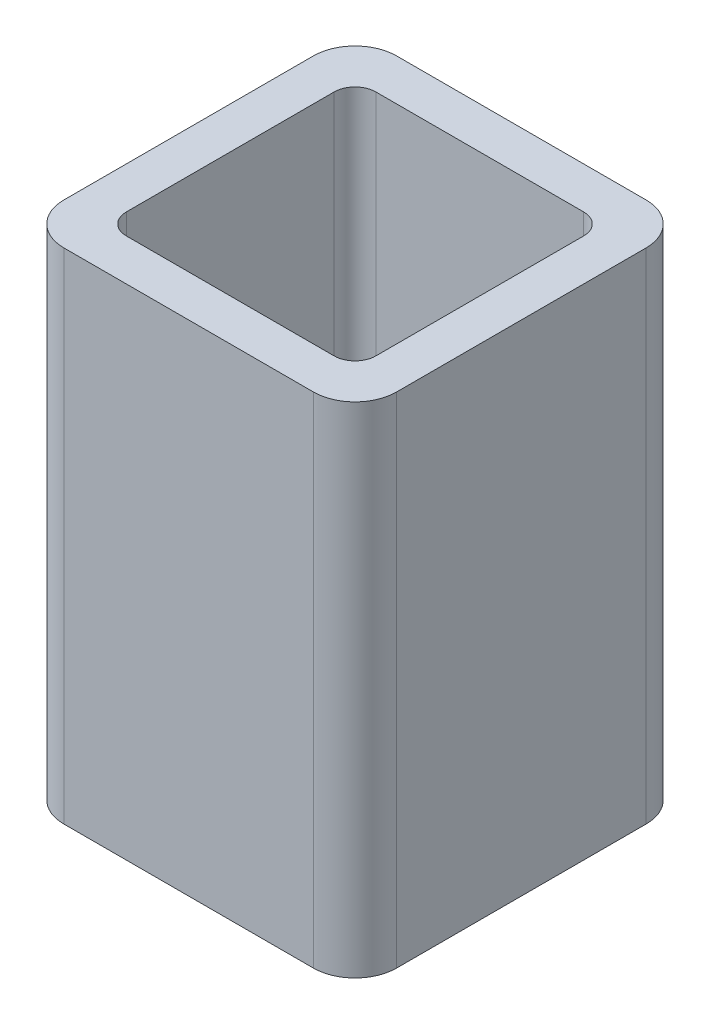
SolidWorks part; units mm, degrees
ref_plane "Front Plane" through (0, 0, 0) normal (0, 0, 1) x (1, 0, 0)
ref_plane "Top Plane" through (0, 0, 0) normal (0, 1, 0) x (1, 0, 0)
ref_plane "Right Plane" through (0, 0, 0) normal (1, 0, 0) x (0, 0, -1)
sketch "Sketch1" plane through (0, 0, 0) normal (0, 1, 0) x (1, 0, 0)
  line L0 (-25, 30) -> (25, 30)
  line L1 (-30, -40) -> (30, -40)
  line L2 (-40, -30) -> (-40, 30)
  line L3 (-30, 40) -> (30, 40)
  line L4 (40, -30) -> (40, 30)
  line L5 (30, -25) -> (30, 25)
  line L6 (-25, -30) -> (25, -30)
  line L7 (-30, -25) -> (-30, 25)
  line L8 (-30, -30) -> (30, -30) construction
  line L9 (-30, -30) -> (-30, 30) construction
  line L10 (30, -30) -> (30, 30) construction
  line L11 (-30, 30) -> (30, 30) construction
  arc A0 (30, -40) -> (40, -30) centre (30, -30) ccw
  arc A1 (-30, -40) -> (-40, -30) centre (-30, -30) cw
  arc A2 (30, 40) -> (40, 30) centre (30, 30) cw
  arc A3 (-40, 30) -> (-30, 40) centre (-30, 30) cw
  arc A4 (-25, 30) -> (-30, 25) centre (-25, 25) ccw
  arc A5 (25, 30) -> (30, 25) centre (25, 25) cw
  arc A6 (30, -25) -> (25, -30) centre (25, -25) cw
  arc A8 (-25, -30) -> (-30, -25) centre (-25, -25) cw
  arc A9 (-30, -30) -> (-30, -30) centre (-30, -30) cw construction
  arc A10 (30, -30) -> (30, -30) centre (30, -30) ccw construction
  arc A11 (30, 30) -> (30, 30) centre (30, 30) cw construction
  arc A12 (-30, 30) -> (-30, 30) centre (-30, 30) cw construction
  point P0 (0, 0)
  dimension "D1" = 10
  dimension "D3" = 5
  dimension "D2" = 10
extrude "Boss-Extrude1" add sketch "Sketch1" along normal mid plane 120
